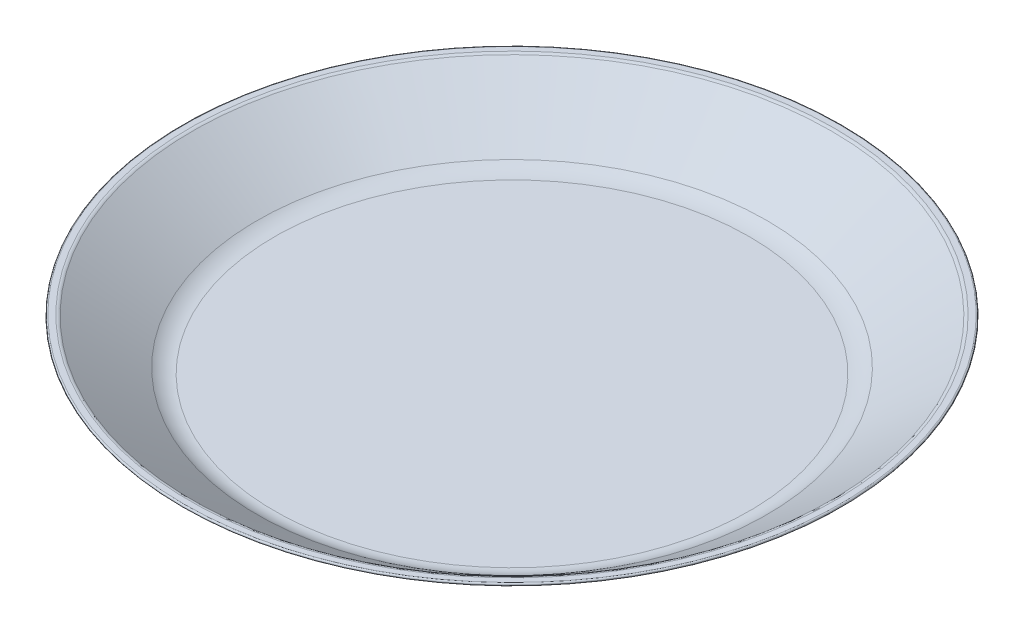
SolidWorks part; units mm, degrees
material "Ceramic Porcelain"
ref_plane "Front Plane" through (0, 0, 0) normal (0, 0, 1) x (1, 0, 0)
ref_plane "Top Plane" through (0, 0, 0) normal (0, 1, 0) x (1, 0, 0)
ref_plane "Right Plane" through (0, 0, 0) normal (1, 0, 0) x (0, 0, -1)
sketch "ProfileS" plane through (0, 0, 0) normal (0, 0, 1) x (1, 0, 0)
  line L0 (0, 0) -> (90.0936, 0)
  line L1 (98.0915, 2.5094) -> (124.7856, 21.0896)
  line L2 (0, 0) -> (0, 22) construction
  line L3 (0, 22) -> (126.0936, 22) construction
  line L4 (0, 2.5) -> (90.0936, 2.5)
  line L5 (96.6633, 4.5613) -> (121.2024, 21.6415)
  line L6 (0, 2.5) -> (0, 0)
  line L7 (124.5, 22) -> (122.345, 22)
  line L8 (98.0915, 2.5094) -> (126.0936, 22) construction
  line L9 (96.6633, 4.5613) -> (124.6654, 24.0519) construction
  line L10 (125, 22) -> (125, 0) construction
  line L11 (126.0936, 22) -> (126.0936, 0) construction
  line L12 (126.0936, 0) -> (0, 0) construction
  line L13 (124.7856, 21.0896) -> (126.0936, 22) construction
  arc A0 (98.0915, 2.5094) -> (90.0936, 0) centre (90.0936, 14) cw
  arc A1 (96.6633, 4.5613) -> (90.0936, 2.5) centre (90.0936, 14) cw
  arc A2 (124.7856, 21.0896) -> (124.5, 22) centre (124.5, 21.5) ccw
  arc A3 (122.345, 22) -> (121.2024, 21.6415) centre (122.345, 20) ccw
  point P18 (121.7174, 22)
  dimension "SWStartRadius" = 14
  dimension "D1" = 0.5
  dimension "D2" = 2
  dimension "Height" = 22
  dimension "SlantedWallWidth" = 36
  dimension "D3" = 125
  dimension "Thickness" = 2.5
revolve "Profile" add sketch "ProfileS" angle 360 about L2
